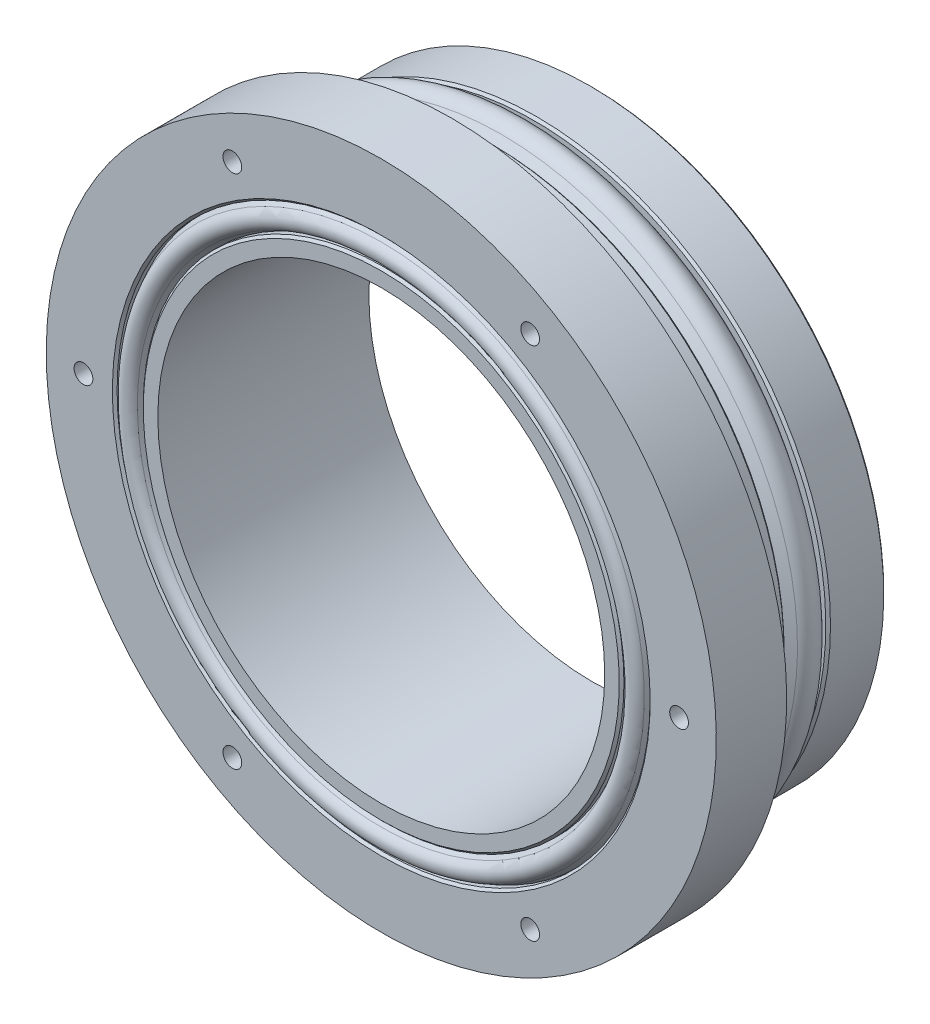
SolidWorks part; units mm, degrees
material "AISI 316 Annealed Stainless Steel Bar (SS)"
ref_plane "Front Plane" through (0, 0, 0) normal (0, 0, 1) x (1, 0, 0)
ref_plane "Top Plane" through (0, 0, 0) normal (0, 1, 0) x (1, 0, 0)
ref_plane "Right Plane" through (0, 0, 0) normal (1, 0, 0) x (0, 0, -1)
sketch "Sketch1" plane through (0, 0, 0) normal (1, 0, 0) x (0, 0, -1)
  line L0 (0, 0) -> (0, 25.4) construction
  line L1 (0, 25.0571) -> (-4.944, 25.0571)
  line L2 (-12, 25.0571) -> (-12, 28.575)
  line L3 (-12, 28.575) -> (-18, 28.575)
  line L4 (-18, 28.575) -> (-18, 22.733)
  line L5 (-18, 19.0571) -> (0, 19.0571)
  line L6 (0, 19.0571) -> (0, 25.0571)
  line L7 (-8.5, 25.0571) -> (-12, 25.0571)
  line L8 (-12, 25.2095) -> (0, 25.2095) construction
  line L9 (0, 0) -> (-18, 0) construction
  line L10 (-18, 0) -> (-18, 19.0571) construction
  line L11 (-8.5, 25.0571) -> (-8.5, 24.2951)
  line L12 (-17.3396, 22.733) -> (-17.9751, 22.4058)
  line L13 (-4.944, 24.2951) -> (-4.944, 25.0571)
  line L14 (-8.5, 24.2951) -> (-7.7635, 25.2643)
  line L15 (-4.944, 24.2951) -> (-5.6805, 25.2643)
  line L16 (-17.3396, 20.4978) -> (-17.9751, 20.825)
  line L17 (0, 25.4) -> (-12, 25.4) construction
  line L18 (-6.722, 25.4) -> (-6.722, 25.781) construction
  line L19 (0, 23.5571) -> (-4, 23.5571) construction
  line L20 (-4, 23.5571) -> (-4, 20.5571) construction
  line L21 (-4, 20.5571) -> (0, 20.5571) construction
  line L22 (-4, 22.0571) -> (0, 22.0571) construction
  line L23 (-18, 20.4978) -> (-17.3396, 20.4978)
  line L24 (-17.3396, 22.733) -> (-17.3396, 20.4978) construction
  line L25 (-17.3396, 22.733) -> (-18, 22.733)
  line L26 (-18, 20.4978) -> (-18, 19.0571)
  line L27 (-18, 26.4) -> (-13, 26.4) construction
  line L28 (-13, 26.4) -> (-13, 24.4) construction
  line L29 (-13, 24.4) -> (-18, 24.4) construction
  line L30 (-13, 25.4) -> (-18, 25.4) construction
  arc A0 (-5.6805, 25.2643) -> (-7.7635, 25.2643) centre (-6.722, 24.4729) ccw
  arc A2 (-17.9751, 22.4058) -> (-17.9751, 20.825) centre (-17.5682, 21.6154) ccw
  point P33 (0, 22.0571)
  dimension "D4" = 2.6162
  dimension "D12" = 3
  dimension "D20" = 1.778
  dimension "D9" = 3.556
  dimension "D1" = 25.4
  dimension "D2" = 3.5
  dimension "D3" = 6
  dimension "D5" = 12
  dimension "D6" = 6
  dimension "D7" = 28.575
  dimension "D8" = 0.762
  dimension "D10" = 19.0571
  dimension "D11" = 50.1142
  dimension "D13" = 4
  dimension "D14" = 0.6604
  dimension "D15" = 2.2352
  dimension "D16" = 20.4978
  dimension "D17" = 2
  dimension "D18" = 25.4
  dimension "D19" = 5
  dimension "D21" = 25.2095
  dimension "D22" = 0.2286
  dimension "D23" = 0.381
revolve "Revolve1" add sketch "Sketch1" angle 360 about L9
sketch "Sketch2" plane through (0, 0, 18) normal (0, 0, 1) x (1, 0, 0)
  circle A0 centre (-25.4, 0) radius 0.8
  circle A1 centre (0, 0) radius 28.575 construction
  circle A2 centre (-12.7, 21.997) radius 0.8
  circle A3 centre (12.7, 21.997) radius 0.8
  circle A4 centre (25.4, 0) radius 0.8
  circle A5 centre (12.7, -21.997) radius 0.8
  circle A6 centre (-12.7, -21.997) radius 0.8
  point P17 (0, 0)
  dimension "D1" = 1.6
  dimension "D2" = 3.175
  dimension "D4" = 50.8
  dimension "D3" = 6
extrude "Cut-Extrude1" cut sketch "Sketch2" against normal blind 3.5
chamfer "Chamfer1" distance 0.2 angle 45 5 edges at (0, 25.0571, 8.5) (0, 25.0571, 0) (0, 22.733, 18) (0, 20.4978, 18) (0, 25.0571, 4.944)
sketch "Sketch3" plane through (0, 0, 0) normal (0, 0, -1) x (-1, 0, 0)
  line L0 (-21.5, 0) -> (0, 0) construction
  line L1 (0, 0) -> (0, 21.5) construction
  line L2 (21.5, 0) -> (0, 0) construction
  line L3 (0, 0) -> (0, -21.5) construction
  circle A0 centre (0, 21.5) radius 1.25
  circle A1 centre (21.5, 0) radius 1.25
  circle A2 centre (0, -21.5) radius 1.25
  circle A3 centre (-21.5, 0) radius 1.25
  circle A4 centre (-21.5, 0) radius 1.5 construction
  dimension "D1" = 2.5
  dimension "D3" = 3
  dimension "D2" = 43
extrude "Cut-Extrude2" cut sketch "Sketch3" against normal blind 4
sketch "Sketch4" plane through (0, 0, 18) normal (0, 0, 1) x (1, 0, 0)
  line L0 (-9.3477, 0) -> (0, 0) construction
  line L1 (0, 0) -> (9.3477, 0) construction
  circle A0 centre (-9.3477, 0) radius 9
  circle A1 centre (9.3477, 0) radius 9
  dimension "D1" = 18
sketch "Sketch5" plane through (0, 0, 0) normal (0, 0, -1) x (-1, 0, 0)
  circle A0 centre (0, 0) radius 21.5 construction
